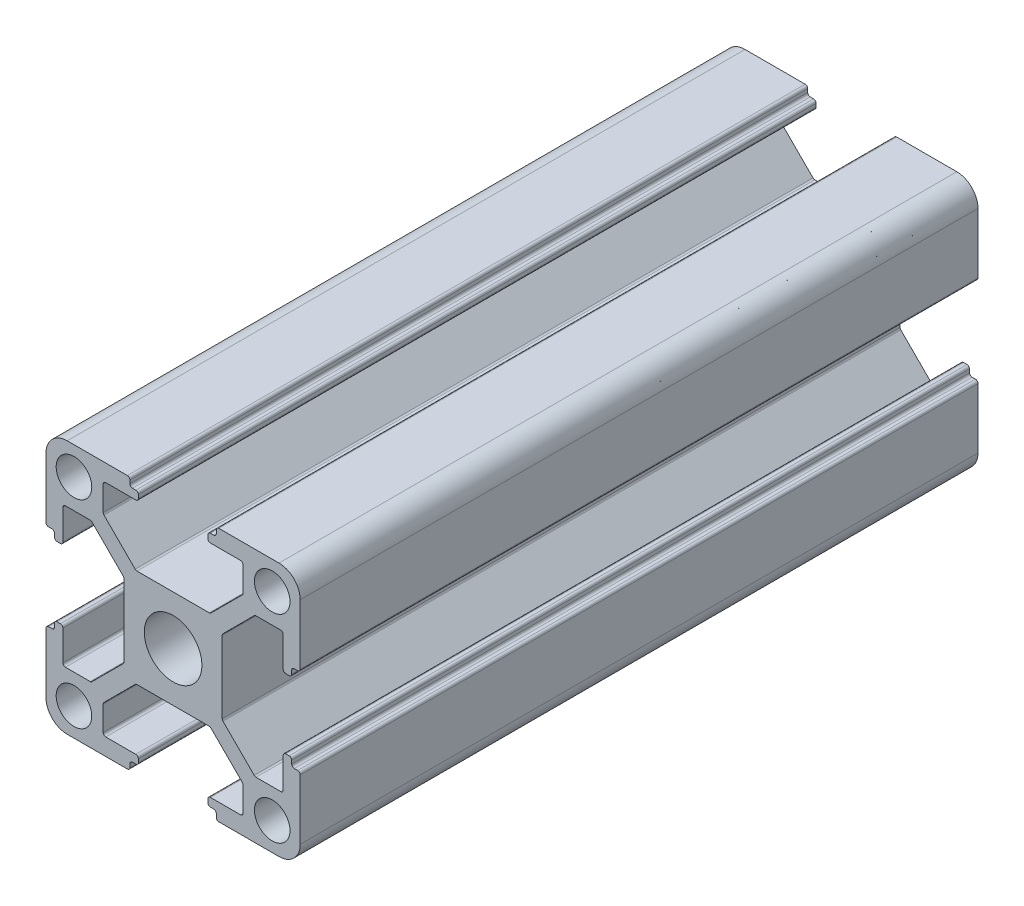
SolidWorks part; units mm, degrees
ref_plane "Alzado" through (0, 0, 0) normal (0, 0, 1) x (1, 0, 0)
ref_plane "Planta" through (0, 0, 0) normal (0, 1, 0) x (1, 0, 0)
ref_plane "Vista lateral" through (0, 0, 0) normal (1, 0, 0) x (0, 0, -1)
ref_plane "Plano1" through (0, 0, -50) normal (0, 0, -1) x (-1, 0, 0)
sketch "Croquis1" plane through (0, 0, -50) normal (0, 0, -1) x (-1, 0, 0)
  line L0 (14.7, -5.1) -> (14.3, -5.1)
  line L1 (14, -4.8) -> (14, -4.4)
  line L2 (13.7, -4.1) -> (13.3, -4.1)
  line L3 (13, -4.4) -> (13, -7.95)
  line L4 (12.7, -8.25) -> (9.7893, -8.25)
  line L5 (9.5772, -8.1622) -> (5.8879, -4.4739)
  line L6 (5.8, -4.2617) -> (5.8, 4.2607)
  line L7 (5.8879, 4.4729) -> (9.5771, 8.1621)
  line L8 (9.7893, 8.25) -> (12.7, 8.25)
  line L9 (13, 7.95) -> (13, 4.4)
  line L10 (13.3, 4.1) -> (13.7, 4.1)
  line L11 (14, 4.4) -> (14, 4.8)
  line L12 (14.3, 5.1) -> (14.7, 5.1)
  line L13 (15, 5.4) -> (15, 12.5)
  line L14 (12.5, 15) -> (5.4, 15)
  line L15 (5.1, 14.7) -> (5.1, 14.3)
  line L16 (4.8, 14) -> (4.4, 14)
  line L17 (4.1, 13.7) -> (4.1, 13.3)
  line L18 (4.4, 13) -> (7.95, 13)
  line L19 (8.25, 12.7) -> (8.25, 9.7883)
  line L20 (8.1621, 9.5761) -> (4.4739, 5.8879)
  line L21 (4.2617, 5.8) -> (-4.2607, 5.8)
  line L22 (-4.4728, 5.8878) -> (-8.1621, 9.5761)
  line L23 (-8.25, 9.7883) -> (-8.25, 12.7)
  line L24 (-7.95, 13) -> (-4.4, 13)
  line L25 (-4.1, 13.3) -> (-4.1, 13.7)
  line L26 (-4.4, 14) -> (-4.8, 14)
  line L27 (-5.1, 14.3) -> (-5.1, 14.7)
  line L28 (-5.4, 15) -> (-12.5, 15)
  line L29 (-15, 12.5) -> (-15, 5.4)
  line L30 (-14.7, 5.1) -> (-14.3, 5.1)
  line L31 (-14, 4.8) -> (-14, 4.4)
  line L32 (-13.7, 4.1) -> (-13.3, 4.1)
  line L33 (-13, 4.4) -> (-13, 7.95)
  line L34 (-12.7, 8.25) -> (-9.7883, 8.25)
  line L35 (-9.5761, 8.1621) -> (-5.8878, 4.4728)
  line L36 (-5.8, 4.2607) -> (-5.8, -4.2617)
  line L37 (-5.8879, -4.4739) -> (-9.5761, -8.1621)
  line L38 (-9.7883, -8.25) -> (-12.7, -8.25)
  line L39 (-13, -7.95) -> (-13, -4.4)
  line L40 (-13.3, -4.1) -> (-13.7, -4.1)
  line L41 (-14, -4.4) -> (-14, -4.8)
  line L42 (-14.3, -5.1) -> (-14.7, -5.1)
  line L43 (-15, -5.4) -> (-15, -12.5)
  line L44 (-12.5, -15) -> (-5.4, -15)
  line L45 (-5.1, -14.7) -> (-5.1, -14.3)
  line L46 (-4.8, -14) -> (-4.4, -14)
  line L47 (-4.1, -13.7) -> (-4.1, -13.3)
  line L48 (-4.4, -13) -> (-7.95, -13)
  line L49 (-8.25, -12.7) -> (-8.25, -9.7893)
  line L50 (-8.1621, -9.5771) -> (-4.4729, -5.8879)
  line L51 (-4.2607, -5.8) -> (4.2617, -5.8)
  line L52 (4.4739, -5.8879) -> (8.1622, -9.5772)
  line L53 (8.25, -9.7893) -> (8.25, -12.7)
  line L54 (7.95, -13) -> (4.4, -13)
  line L55 (4.1, -13.3) -> (4.1, -13.7)
  line L56 (4.4, -14) -> (4.8, -14)
  line L57 (5.1, -14.3) -> (5.1, -14.7)
  line L58 (5.4, -15) -> (12.5, -15)
  line L59 (15, -12.5) -> (15, -5.4)
  arc A0 (15, -5.4) -> (14.7, -5.1) centre (14.7, -5.4) ccw
  arc A1 (14.3, -5.1) -> (14, -4.8) centre (14.3, -4.8) cw
  arc A2 (14, -4.4) -> (13.7, -4.1) centre (13.7, -4.4) ccw
  arc A3 (13.3, -4.1) -> (13, -4.4) centre (13.3, -4.4) ccw
  arc A4 (13, -7.95) -> (12.7, -8.25) centre (12.7, -7.95) cw
  arc A5 (9.7893, -8.25) -> (9.5772, -8.1622) centre (9.7893, -7.95) cw
  arc A6 (5.8879, -4.4739) -> (5.8, -4.2617) centre (6.1, -4.2617) cw
  arc A7 (5.8, 4.2607) -> (5.8879, 4.4729) centre (6.1, 4.2607) cw
  arc A8 (9.5771, 8.1621) -> (9.7893, 8.25) centre (9.7893, 7.95) cw
  arc A9 (12.7, 8.25) -> (13, 7.95) centre (12.7, 7.95) cw
  arc A10 (13, 4.4) -> (13.3, 4.1) centre (13.3, 4.4) ccw
  arc A11 (13.7, 4.1) -> (14, 4.4) centre (13.7, 4.4) ccw
  arc A12 (14, 4.8) -> (14.3, 5.1) centre (14.3, 4.8) cw
  arc A13 (14.7, 5.1) -> (15, 5.4) centre (14.7, 5.4) ccw
  arc A14 (15, 12.5) -> (12.5, 15) centre (12.5, 12.5) ccw
  arc A15 (5.4, 15) -> (5.1, 14.7) centre (5.4, 14.7) ccw
  arc A16 (5.1, 14.3) -> (4.8, 14) centre (4.8, 14.3) cw
  arc A17 (4.4, 14) -> (4.1, 13.7) centre (4.4, 13.7) ccw
  arc A18 (4.1, 13.3) -> (4.4, 13) centre (4.4, 13.3) ccw
  arc A19 (7.95, 13) -> (8.25, 12.7) centre (7.95, 12.7) cw
  arc A20 (8.25, 9.7883) -> (8.1621, 9.5761) centre (7.95, 9.7883) cw
  arc A21 (4.4739, 5.8879) -> (4.2617, 5.8) centre (4.2617, 6.1) cw
  arc A22 (-4.2607, 5.8) -> (-4.4728, 5.8878) centre (-4.2607, 6.1) cw
  arc A23 (-8.1621, 9.5761) -> (-8.25, 9.7883) centre (-7.95, 9.7883) cw
  arc A24 (-8.25, 12.7) -> (-7.95, 13) centre (-7.95, 12.7) cw
  arc A25 (-4.4, 13) -> (-4.1, 13.3) centre (-4.4, 13.3) ccw
  arc A26 (-4.1, 13.7) -> (-4.4, 14) centre (-4.4, 13.7) ccw
  arc A27 (-4.8, 14) -> (-5.1, 14.3) centre (-4.8, 14.3) cw
  arc A28 (-5.1, 14.7) -> (-5.4, 15) centre (-5.4, 14.7) ccw
  arc A29 (-12.5, 15) -> (-15, 12.5) centre (-12.5, 12.5) ccw
  arc A30 (-15, 5.4) -> (-14.7, 5.1) centre (-14.7, 5.4) ccw
  arc A31 (-14.3, 5.1) -> (-14, 4.8) centre (-14.3, 4.8) cw
  arc A32 (-14, 4.4) -> (-13.7, 4.1) centre (-13.7, 4.4) ccw
  arc A33 (-13.3, 4.1) -> (-13, 4.4) centre (-13.3, 4.4) ccw
  arc A34 (-13, 7.95) -> (-12.7, 8.25) centre (-12.7, 7.95) cw
  arc A35 (-9.7883, 8.25) -> (-9.5761, 8.1621) centre (-9.7883, 7.95) cw
  arc A36 (-5.8878, 4.4728) -> (-5.8, 4.2607) centre (-6.1, 4.2607) cw
  arc A37 (-5.8, -4.2617) -> (-5.8879, -4.4739) centre (-6.1, -4.2617) cw
  arc A38 (-9.5761, -8.1621) -> (-9.7883, -8.25) centre (-9.7883, -7.95) cw
  arc A39 (-12.7, -8.25) -> (-13, -7.95) centre (-12.7, -7.95) cw
  arc A40 (-13, -4.4) -> (-13.3, -4.1) centre (-13.3, -4.4) ccw
  arc A41 (-13.7, -4.1) -> (-14, -4.4) centre (-13.7, -4.4) ccw
  arc A42 (-14, -4.8) -> (-14.3, -5.1) centre (-14.3, -4.8) cw
  arc A43 (-14.7, -5.1) -> (-15, -5.4) centre (-14.7, -5.4) ccw
  arc A44 (-15, -12.5) -> (-12.5, -15) centre (-12.5, -12.5) ccw
  arc A45 (-5.4, -15) -> (-5.1, -14.7) centre (-5.4, -14.7) ccw
  arc A46 (-5.1, -14.3) -> (-4.8, -14) centre (-4.8, -14.3) cw
  arc A47 (-4.4, -14) -> (-4.1, -13.7) centre (-4.4, -13.7) ccw
  arc A48 (-4.1, -13.3) -> (-4.4, -13) centre (-4.4, -13.3) ccw
  arc A49 (-7.95, -13) -> (-8.25, -12.7) centre (-7.95, -12.7) cw
  arc A50 (-8.25, -9.7893) -> (-8.1621, -9.5771) centre (-7.95, -9.7893) cw
  arc A51 (-4.4729, -5.8879) -> (-4.2607, -5.8) centre (-4.2607, -6.1) cw
  arc A52 (4.2617, -5.8) -> (4.4739, -5.8879) centre (4.2617, -6.1) cw
  arc A53 (8.1622, -9.5772) -> (8.25, -9.7893) centre (7.95, -9.7893) cw
  arc A54 (8.25, -12.7) -> (7.95, -13) centre (7.95, -12.7) cw
  arc A55 (4.4, -13) -> (4.1, -13.3) centre (4.4, -13.3) ccw
  arc A56 (4.1, -13.7) -> (4.4, -14) centre (4.4, -13.7) ccw
  arc A57 (4.8, -14) -> (5.1, -14.3) centre (4.8, -14.3) cw
  arc A58 (5.1, -14.7) -> (5.4, -15) centre (5.4, -14.7) ccw
  arc A59 (12.5, -15) -> (15, -12.5) centre (12.5, -12.5) ccw
  circle A60 centre (-11.7, 11.7) radius 2.1
  circle A61 centre (-11.7, -11.7) radius 2.1
  circle A62 centre (0, 0) radius 3.4
  circle A63 centre (11.7, 11.7) radius 2.1
  circle A64 centre (11.7, -11.7) radius 2.1
extrude "Saliente-Extruir1" add sketch "Croquis1" against normal blind 400
sketch "Croquis2" plane through (0, 0, 350) normal (0, 0, 1) x (1, 0, 0)
  line L1 (-17.9021, 16.0696) -> (20.5199, 16.0696)
  line L2 (-17.9021, 16.0696) -> (-17.9021, -15.546)
  line L3 (-17.9021, -15.546) -> (20.5199, -15.546)
  line L4 (20.5199, 16.0696) -> (20.5199, -15.546)
extrude "Cortar-Extruir1" cut sketch "Croquis2" against normal blind 320
